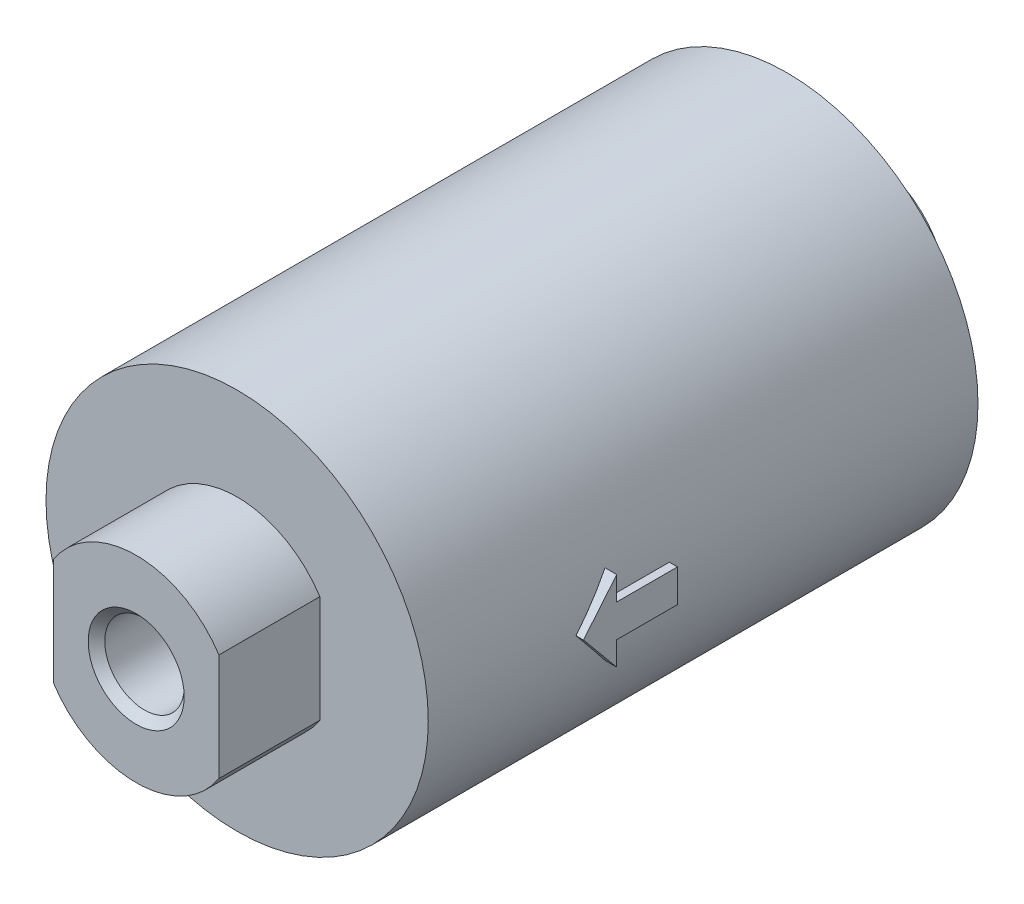
SolidWorks part; units mm, degrees
ref_plane "Front Plane" through (0, 0, 0) normal (0, 0, 1) x (1, 0, 0)
ref_plane "Top Plane" through (0, 0, 0) normal (0, 1, 0) x (1, 0, 0)
ref_plane "Right Plane" through (0, 0, 0) normal (1, 0, 0) x (0, 0, -1)
sketch "Sketch1" plane through (0, 0, 0) normal (0, 0, 1) x (1, 0, 0)
  circle A0 centre (0, 0) radius 11.55
  dimension "D1" = 23.1
extrude "Boss-Extrude1" add sketch "Sketch1" along normal blind 33.22
sketch "Sketch2" plane through (0, 0, 33.22) normal (0, 0, 1) x (1, 0, 0)
  line L0 (5, 3.2345) -> (5, -3.2345)
  line L1 (0, 0) -> (0, 5.955) construction
  line L2 (-5, 3.2345) -> (-5, -3.2345)
  arc A0 (5, 3.2345) -> (-5, 3.2345) centre (0, 0) ccw
  arc A1 (-5, -3.2345) -> (5, -3.2345) centre (0, 0) ccw
  dimension "D1" = 11.91
  dimension "D2" = 10
extrude "Boss-Extrude2" add sketch "Sketch2" along normal blind 6.1
sketch "Sketch3" plane through (0, 0, 39.32) normal (0, 0, 1) x (1, 0, 0)
  circle A0 centre (0, 0) radius 2.4
  dimension "D1" = 4.8
extrude "Cut-Extrude1" cut sketch "Sketch3" against normal blind 8.3
chamfer "Chamfer1" distance 0.5 angle 45 1 edges at (2.4, 0, 39.32)
sketch "Sketch4" plane through (0, 0, 0) normal (0, 0, -1) x (-1, 0, 0)
  line L0 (4.5, 2.1794) -> (4.5, -2.1794)
  line L1 (0, 0) -> (0, 5) construction
  line L2 (-4.5, 2.1794) -> (-4.5, -2.1794)
  arc A0 (-4.5, -2.1794) -> (4.5, -2.1794) centre (0, 0) ccw
  arc A1 (4.5, 2.1794) -> (-4.5, 2.1794) centre (0, 0) ccw
  circle A2 centre (0, 0) radius 2.45
  dimension "D1" = 10
  dimension "D3" = 4.9
  dimension "D2" = 9
extrude "Boss-Extrude3" add sketch "Sketch4" along normal blind 4.7
sketch "Sketch5" plane through (4.5, 0, 0) normal (1, 0, 0) x (0, 0, -1)
  line L0 (-24.2915, 0) -> (-22.2814, 2.4229)
  line L1 (-22.2814, 2.4229) -> (-22.2814, 0.9871)
  line L2 (-22.2814, 0.9871) -> (-18.6077, 0.9871)
  line L3 (-18.6077, 0.9871) -> (-18.6077, -0.9871)
  line L4 (-18.6077, 0) -> (-24.2915, 0) construction
  line L5 (-22.2814, -0.9871) -> (-18.6077, -0.9871)
  line L6 (-22.2814, -2.4229) -> (-22.2814, -0.9871)
  line L7 (-24.2915, 0) -> (-22.2814, -2.4229)
extrude "Boss-Extrude4" add sketch "Sketch5" against normal up to surface (0.707 mm away) from offset 7.5
